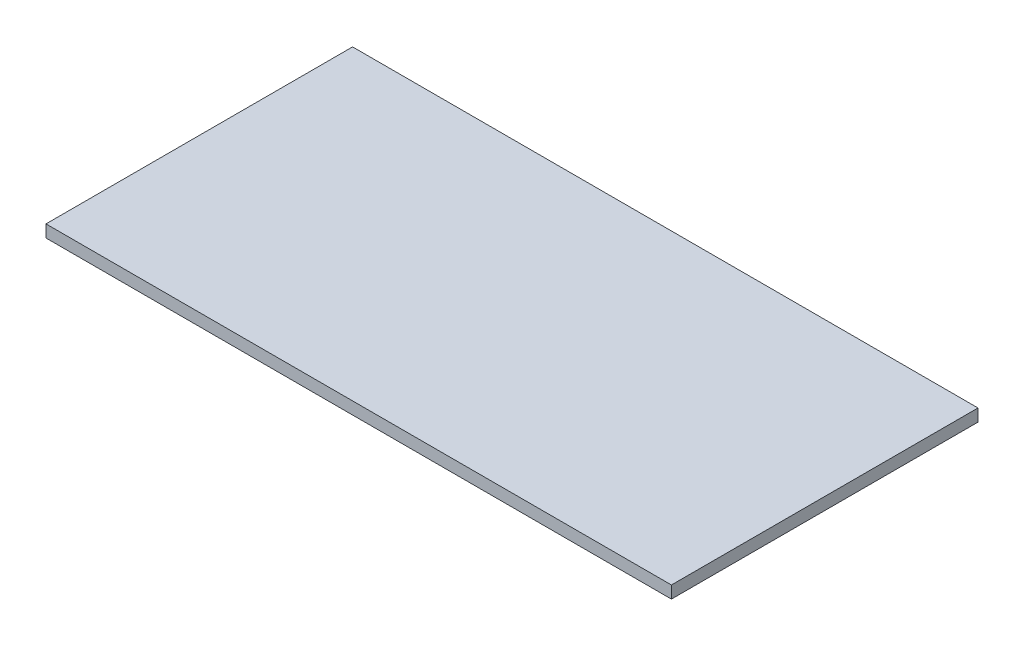
SolidWorks part; units mm, degrees
ref_plane "Front Plane" through (0, 0, 0) normal (0, 0, 1) x (1, 0, 0)
ref_plane "Top Plane" through (0, 0, 0) normal (0, 1, 0) x (1, 0, 0)
ref_plane "Right Plane" through (0, 0, 0) normal (1, 0, 0) x (0, 0, -1)
sketch "Sketch1" plane through (0, 0, 0) normal (0, 1, 0) x (1, 0, 0)
  line L1 (-362.4558, 157.8134) -> (285.2442, 157.8134)
  line L2 (-362.4558, 157.8134) -> (-362.4558, -159.6866)
  line L3 (-362.4558, -159.6866) -> (285.2442, -159.6866)
  line L4 (285.2442, 157.8134) -> (285.2442, -159.6866)
  dimension "D1" = 317.5
  dimension "D2" = 647.7
extrude "Boss-Extrude1" add sketch "Sketch1" along normal blind 12.7
